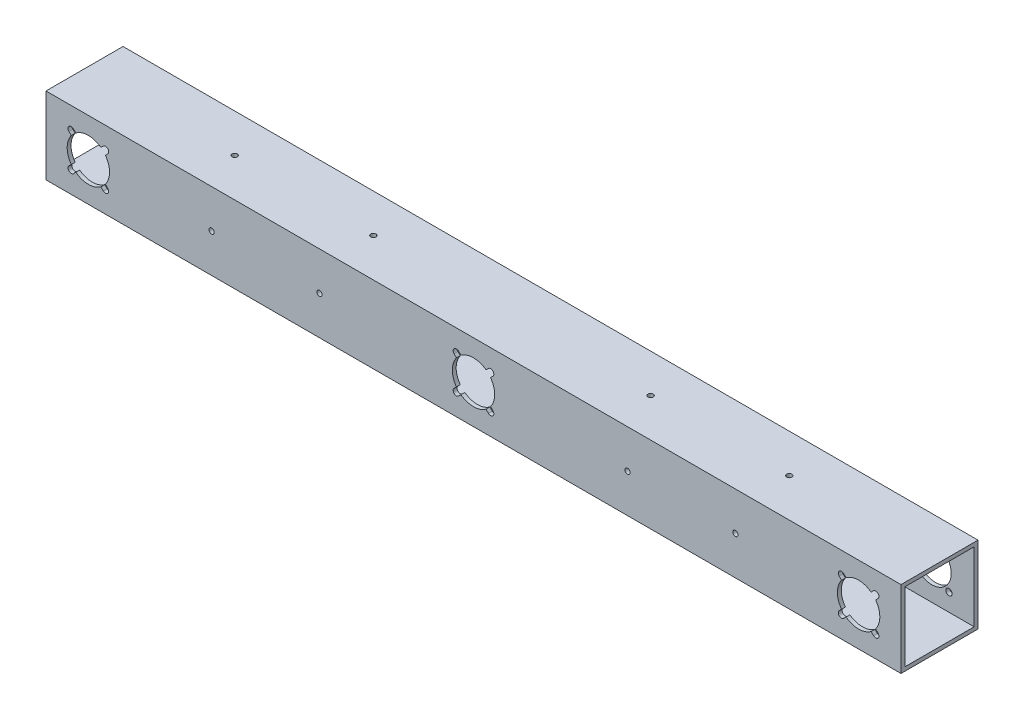
SolidWorks part; units mm, degrees
material "6061-T6 (SS)"
ref_plane "Front Plane" through (0, 0, 0) normal (0, 0, 1) x (1, 0, 0)
ref_plane "Top Plane" through (0, 0, 0) normal (0, 1, 0) x (1, 0, 0)
ref_plane "Right Plane" through (0, 0, 0) normal (1, 0, 0) x (0, 0, -1)
sketch "Sketch1" plane through (0, 0, 0) normal (1, 0, 0) x (0, 0, -1)
  line L1 (-31.75, -31.75) -> (31.75, -31.75)
  line L2 (-31.75, -31.75) -> (-31.75, 31.75)
  line L3 (-31.75, 31.75) -> (31.75, 31.75)
  line L4 (31.75, -31.75) -> (31.75, 31.75)
  point P0 (0, 0)
  dimension "D1" = 63.5
extrude "Boss-Extrude1" add sketch "Sketch1" along normal blind 704.85
sketch "Sketch2" plane through (704.85, 0, 0) normal (1, 0, 0) x (0, 0, -1)
  line L0 (31.75, 31.75) -> (-31.75, 31.75) construction
  line L1 (-28.575, -28.575) -> (28.575, -28.575)
  line L2 (-28.575, -28.575) -> (-28.575, 28.575)
  line L3 (-28.575, 28.575) -> (28.575, 28.575)
  line L4 (28.575, -28.575) -> (28.575, 28.575)
  line L5 (-28.575, -28.575) -> (28.575, 28.575) construction
  line L6 (-28.575, 28.575) -> (28.575, -28.575) construction
  point P0 (0, 0)
  dimension "D1" = 3.175
extrude "Cut-Extrude1" cut sketch "Sketch2" against normal through all
sketch "Sketch3" plane through (0, 0, 31.75) normal (0, 0, 1) x (1, 0, 0)
  line L0 (0, 0) -> (704.85, 0) construction
  line L1 (704.85, 31.75) -> (704.85, -31.75) construction
  line L2 (352.425, -31.75) -> (352.425, 31.75) construction
  line L3 (704.85, -31.75) -> (0, -31.75) construction
  line L4 (704.85, 31.75) -> (0, 31.75) construction
  circle A0 centre (352.425, 0) radius 17.4625
  circle A1 centre (34.925, 0) radius 17.4625
  circle A2 centre (669.925, 0) radius 17.4625
  dimension "D1" = 34.925
  dimension "D2" = 317.5
  dimension "D3" = 317.5
extrude "Cut-Extrude2" cut sketch "Sketch3" against normal up to next
sketch "Sketch8" plane through (0, 31.75, 0) normal (0, 1, 0) x (1, 0, 0)
  line L0 (0, 0) -> (704.85, 0) construction
  line L1 (704.85, 31.75) -> (704.85, -31.75) construction
  line L2 (352.425, 0) -> (352.425, 31.75) construction
  line L3 (704.85, 31.75) -> (0, 31.75) construction
  circle A0 centre (466.725, 0) radius 2.1526
  circle A1 centre (123.825, 0) radius 2.1526
  circle A2 centre (581.025, 0) radius 2.1526
  circle A3 centre (238.125, 0) radius 2.1526
  dimension "D1" = 4.3053
  dimension "D2" = 114.3
  dimension "D3" = 228.6
extrude "Cut-Extrude6" cut sketch "Sketch8" against normal through all
sketch "Sketch10" plane through (0, 0, 31.75) normal (0, 0, 1) x (1, 0, 0)
  line L0 (0, 0) -> (704.85, 0) construction
  line L1 (704.85, 31.75) -> (704.85, -31.75) construction
  line L2 (352.425, 0) -> (352.425, 31.75) construction
  line L3 (704.85, 31.75) -> (0, 31.75) construction
  circle A0 centre (225.425, 0) radius 2.1527
  circle A1 centre (568.325, 0) radius 2.1526
  circle A2 centre (136.525, 0) radius 2.1527
  circle A3 centre (479.425, 0) radius 2.1526
  dimension "D1" = 4.3053
  dimension "D2" = 127
  dimension "D3" = 215.9
extrude "Cut-Extrude7" cut sketch "Sketch10" against normal through all
sketch "Sketch13" plane through (0, 0, -31.75) normal (0, 0, -1) x (-1, 0, 0)
  line L0 (0, 0) -> (-704.85, 0) construction
  line L1 (-704.85, -31.75) -> (-704.85, 31.75) construction
  line L2 (-352.425, 0) -> (-34.925, 0) construction
  line L3 (-352.425, 0) -> (-669.925, 0) construction
  circle A0 centre (-352.425, 0) radius 16
  circle A1 centre (-34.925, 0) radius 16
  circle A2 centre (-669.925, 0) radius 16
  dimension "D3" = 32
  dimension "D1" = 317.5
  dimension "D2" = 317.5
extrude "Cut-Extrude9" cut sketch "Sketch13" against normal up to next
sketch "Sketch14" plane through (0, 0, -31.75) normal (0, 0, -1) x (-1, 0, 0)
  line L0 (0, 0) -> (-704.85, 0) construction
  line L1 (-704.85, -31.75) -> (-704.85, 31.75) construction
  line L2 (-352.425, 0) -> (-34.925, 0) construction
  line L3 (-669.925, 0) -> (-352.425, 0) construction
  line L4 (-352.425, 0) -> (-338.2829, 14.1421) construction
  line L5 (-669.925, 0) -> (-655.7829, 14.1421) construction
  line L6 (-34.925, 0) -> (-20.7829, 14.1421) construction
  line L7 (-352.425, 0) -> (-338.2829, -14.1421) construction
  line L8 (-352.425, 0) -> (-366.5671, -14.1421) construction
  line L9 (-352.425, 0) -> (-366.5671, 14.1421) construction
  line L10 (-34.925, 0) -> (-20.7829, -14.1421) construction
  line L11 (-34.925, 0) -> (-49.0671, -14.1421) construction
  line L12 (-34.925, 0) -> (-49.0671, 14.1421) construction
  line L13 (-669.925, 0) -> (-655.7829, -14.1421) construction
  line L14 (-669.925, 0) -> (-684.0671, -14.1421) construction
  line L15 (-669.925, 0) -> (-684.0671, 14.1421) construction
  circle A0 centre (-655.7829, 14.1421) radius 2.625
  circle A1 centre (-338.2829, 14.1421) radius 2.625
  circle A2 centre (-20.7829, 14.1421) radius 2.625
  circle A3 centre (-352.425, 0) radius 16
  circle A4 centre (-34.925, 0) radius 16
  circle A5 centre (-669.925, 0) radius 16
  circle A6 centre (-338.2829, -14.1421) radius 2.625
  circle A7 centre (-366.5671, -14.1421) radius 2.625
  circle A8 centre (-366.5671, 14.1421) radius 2.625
  circle A9 centre (-20.7829, -14.1421) radius 2.625
  circle A10 centre (-49.0671, -14.1421) radius 2.625
  circle A11 centre (-49.0671, 14.1421) radius 2.625
  circle A12 centre (-655.7829, -14.1421) radius 2.625
  circle A13 centre (-684.0671, -14.1421) radius 2.625
  circle A14 centre (-684.0671, 14.1421) radius 2.625
  point P28 (-352.425, 0)
  point P35 (-34.925, 0)
  point P42 (-669.925, 0)
  dimension "D4" = 5.25
  dimension "D1" = 45
  dimension "D2" = 45
  dimension "D3" = 45
  dimension "D5" = 20
  dimension "D6" = 4
  dimension "D7" = 4
  dimension "D8" = 4
extrude "Cut-Extrude10" cut sketch "Sketch14" against normal up to next (3.175 mm away)
sketch "Sketch15" plane through (0, 0, 31.75) normal (0, 0, 1) x (1, 0, 0)
  line L0 (0, 0) -> (704.85, 0) construction
  line L1 (50.9233, 12.286) -> (47.211, 15.9983) construction
  line L2 (0, 31.75) -> (0, -31.75) construction
  line L3 (704.85, 31.75) -> (704.85, -31.75) construction
  line L4 (352.425, 0) -> (352.425, 31.75) construction
  line L5 (704.85, 31.75) -> (0, 31.75) construction
  line L6 (34.925, 0) -> (352.425, 0) construction
  line L7 (193.675, 0) -> (193.675, 31.75) construction
  line L8 (669.925, 0) -> (352.425, 0) construction
  line L9 (511.175, 0) -> (511.175, 31.75) construction
  line L10 (352.425, 0) -> (366.5671, 14.1421) construction
  line L11 (364.711, -15.9983) -> (362.7764, -14.0637)
  line L12 (49.0671, 14.1421) -> (50.9233, 12.286) construction
  line L13 (366.5671, 14.1421) -> (364.711, 15.9983) construction
  line L14 (364.711, 15.9983) -> (368.4233, 12.286) construction
  line L15 (368.4233, 12.286) -> (366.4887, 10.3514)
  line L16 (364.711, 15.9983) -> (362.7764, 14.0637)
  line L17 (368.4233, -12.286) -> (366.4887, -10.3514)
  line L18 (352.425, 0) -> (366.5671, -14.1421) construction
  line L19 (366.5671, -14.1421) -> (368.4233, -12.286) construction
  line L20 (368.4233, -12.286) -> (364.711, -15.9983) construction
  line L21 (336.4267, -12.286) -> (338.3613, -10.3514)
  line L22 (340.139, -15.9983) -> (342.0736, -14.0637)
  line L23 (352.425, 0) -> (338.2829, -14.1421) construction
  line L24 (338.2829, -14.1421) -> (340.139, -15.9983) construction
  line L25 (340.139, -15.9983) -> (336.4267, -12.286) construction
  line L26 (340.139, 15.9983) -> (342.0736, 14.0637)
  line L27 (336.4267, 12.286) -> (338.3613, 10.3514)
  line L28 (352.425, 0) -> (338.2829, 14.1421) construction
  line L29 (338.2829, 14.1421) -> (336.4267, 12.286) construction
  line L30 (336.4267, 12.286) -> (340.139, 15.9983) construction
  line L31 (34.925, 0) -> (49.0671, 14.1421) construction
  line L32 (47.211, -15.9983) -> (50.9233, -12.286) construction
  line L33 (49.0671, -14.1421) -> (47.211, -15.9983) construction
  line L34 (34.925, 0) -> (49.0671, -14.1421) construction
  line L35 (18.9267, -12.286) -> (22.639, -15.9983) construction
  line L36 (20.7829, -14.1421) -> (18.9267, -12.286) construction
  line L37 (34.925, 0) -> (20.7829, -14.1421) construction
  line L38 (22.639, 15.9983) -> (18.9267, 12.286) construction
  line L39 (20.7829, 14.1421) -> (22.639, 15.9983) construction
  line L40 (34.925, 0) -> (20.7829, 14.1421) construction
  line L41 (34.925, 0) -> (34.925, 31.75) construction
  line L42 (50.9233, 12.286) -> (48.9887, 10.3514)
  line L43 (47.211, 15.9983) -> (45.2764, 14.0637)
  line L44 (47.211, -15.9983) -> (45.2764, -14.0637)
  line L45 (50.9233, -12.286) -> (48.9887, -10.3514)
  line L46 (18.9267, -12.286) -> (20.8613, -10.3514)
  line L47 (22.639, 15.9983) -> (24.5736, 14.0637)
  line L48 (18.9267, 12.286) -> (20.8613, 10.3514)
  line L49 (22.639, -15.9983) -> (24.5736, -14.0637)
  line L50 (685.9233, 12.286) -> (682.211, 15.9983) construction
  line L51 (684.0671, 14.1421) -> (685.9233, 12.286) construction
  line L52 (669.925, 0) -> (684.0671, 14.1421) construction
  line L53 (682.211, -15.9983) -> (685.9233, -12.286) construction
  line L54 (684.0671, -14.1421) -> (682.211, -15.9983) construction
  line L55 (669.925, 0) -> (684.0671, -14.1421) construction
  line L56 (653.9267, -12.286) -> (657.639, -15.9983) construction
  line L57 (655.7829, -14.1421) -> (653.9267, -12.286) construction
  line L58 (669.925, 0) -> (655.7829, -14.1421) construction
  line L59 (657.639, 15.9983) -> (653.9267, 12.286) construction
  line L60 (655.7829, 14.1421) -> (657.639, 15.9983) construction
  line L61 (669.925, 0) -> (655.7829, 14.1421) construction
  line L62 (669.925, 0) -> (669.925, 31.75) construction
  line L63 (685.9233, 12.286) -> (683.9887, 10.3514)
  line L64 (682.211, 15.9983) -> (680.2764, 14.0637)
  line L65 (682.211, -15.9983) -> (680.2764, -14.0637)
  line L66 (685.9233, -12.286) -> (683.9887, -10.3514)
  line L67 (653.9267, -12.286) -> (655.8613, -10.3514)
  line L68 (657.639, 15.9983) -> (659.5736, 14.0637)
  line L69 (653.9267, 12.286) -> (655.8613, 10.3514)
  line L70 (657.639, -15.9983) -> (659.5736, -14.0637)
  arc A0 (362.7764, 14.0637) -> (342.0736, 14.0637) centre (352.425, 0) ccw
  arc A1 (368.4233, 12.286) -> (364.711, 15.9983) centre (366.5671, 14.1421) ccw
  arc A2 (364.711, -15.9983) -> (368.4233, -12.286) centre (366.5671, -14.1421) ccw
  arc A3 (336.4267, -12.286) -> (340.139, -15.9983) centre (338.2829, -14.1421) ccw
  arc A4 (340.139, 15.9983) -> (336.4267, 12.286) centre (338.2829, 14.1421) ccw
  arc A5 (338.3613, 10.3514) -> (338.3613, -10.3514) centre (352.425, 0) ccw
  arc A6 (342.0736, -14.0637) -> (362.7764, -14.0637) centre (352.425, 0) ccw
  arc A7 (366.4887, -10.3514) -> (366.4887, 10.3514) centre (352.425, 0) ccw
  arc A8 (20.8613, -10.3514) -> (20.8613, 10.3514) centre (34.925, 0) cw
  arc A9 (45.2764, -14.0637) -> (24.5736, -14.0637) centre (34.925, 0) cw
  arc A10 (48.9887, 10.3514) -> (48.9887, -10.3514) centre (34.925, 0) cw
  arc A11 (47.211, 15.9983) -> (50.9233, 12.286) centre (49.0671, 14.1421) cw
  arc A13 (50.9233, -12.286) -> (47.211, -15.9983) centre (49.0671, -14.1421) cw
  arc A14 (22.639, -15.9983) -> (18.9267, -12.286) centre (20.7829, -14.1421) cw
  arc A15 (18.9267, 12.286) -> (22.639, 15.9983) centre (20.7829, 14.1421) cw
  arc A16 (24.5736, 14.0637) -> (45.2764, 14.0637) centre (34.925, 0) cw
  arc A17 (655.8613, -10.3514) -> (655.8613, 10.3514) centre (669.925, 0) cw
  arc A18 (680.2764, -14.0637) -> (659.5736, -14.0637) centre (669.925, 0) cw
  arc A19 (683.9887, 10.3514) -> (683.9887, -10.3514) centre (669.925, 0) cw
  arc A20 (682.211, 15.9983) -> (685.9233, 12.286) centre (684.0671, 14.1421) cw
  arc A21 (685.9233, -12.286) -> (682.211, -15.9983) centre (684.0671, -14.1421) cw
  arc A22 (657.639, -15.9983) -> (653.9267, -12.286) centre (655.7829, -14.1421) cw
  arc A23 (653.9267, 12.286) -> (657.639, 15.9983) centre (655.7829, 14.1421) cw
  arc A24 (659.5736, 14.0637) -> (680.2764, 14.0637) centre (669.925, 0) cw
  point P43 (352.425, 0)
  dimension "D2" = 45
  dimension "D3" = 5.25
  dimension "D7" = 17.4625
  dimension "D1" = 20
  dimension "D4" = 90
  dimension "D5" = 5.25
  dimension "D8" = 2.7359
  dimension "D6" = 4
extrude "Cut-Extrude11" cut sketch "Sketch15" against normal up to next
sketch "Sketch17" plane through (0, -31.75, 0) normal (0, -1, 0) x (1, 0, 0)
  line L0 (0, 0) -> (704.85, 0) construction
  line L1 (704.85, 31.75) -> (704.85, -31.75) construction
  line L2 (342.9, 0) -> (361.95, 0)
  line L3 (342.9, -25.4) -> (361.95, -25.4)
  line L4 (342.9, -25.4) -> (342.9, 0)
  line L6 (361.95, -25.4) -> (361.95, 0)
  line L7 (342.9, -25.4) -> (352.425, 0) construction
  line L8 (352.425, 0) -> (361.95, -25.4) construction
  point P5 (352.425, 0)
extrude "Cut-Extrude13" cut sketch "Sketch17" against normal up to next
